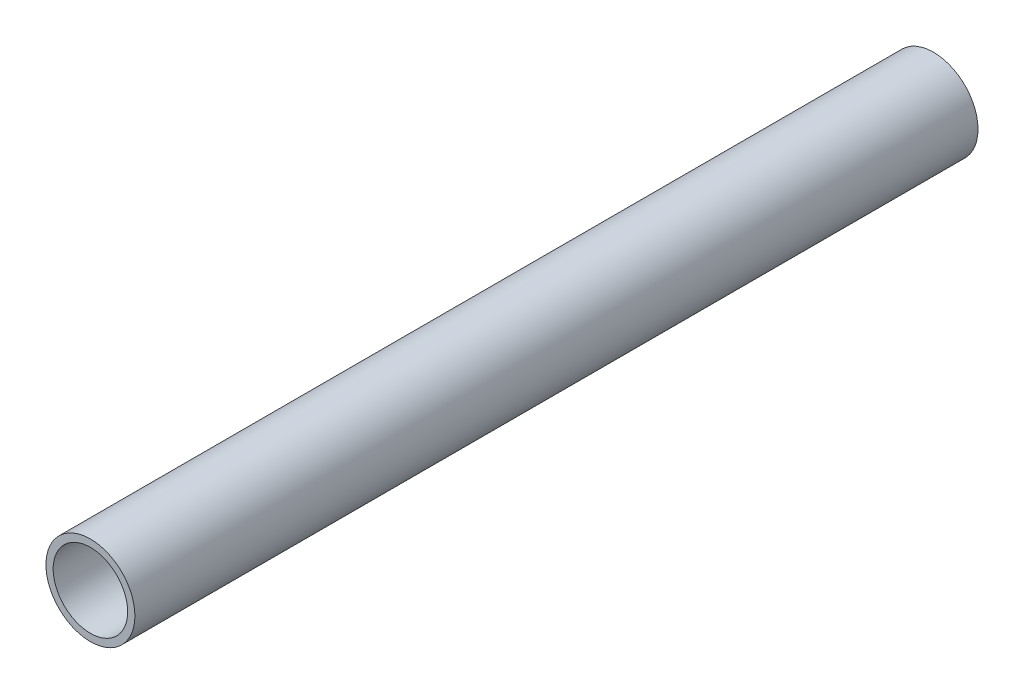
SolidWorks part; units mm, degrees
ref_plane "Front Plane" through (0, 0, 0) normal (0, 0, 1) x (1, 0, 0)
ref_plane "Top Plane" through (0, 0, 0) normal (0, 1, 0) x (1, 0, 0)
ref_plane "Right Plane" through (0, 0, 0) normal (1, 0, 0) x (0, 0, -1)
sketch "Sketch1" plane through (0, 0, 0) normal (0, 0, 1) x (1, 0, 0)
  circle A0 centre (0, 0) radius 24.13
  circle A1 centre (0, 0) radius 20.193
  dimension "D1" = 48.26
  dimension "D2" = 40.386
extrude "Boss-Extrude1" add sketch "Sketch1" along normal blind 457.2
